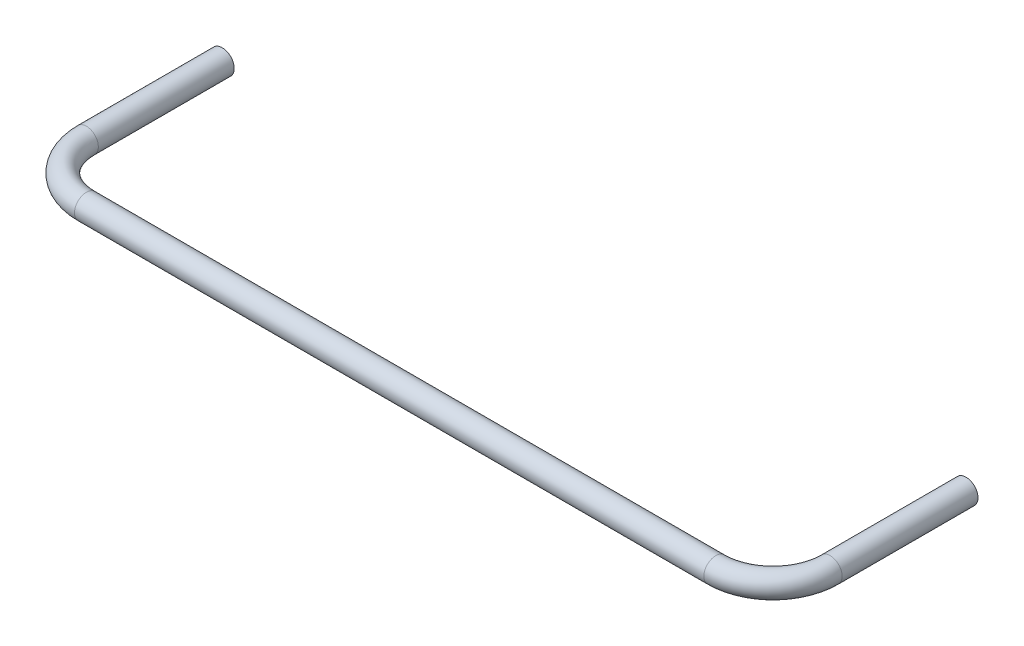
SolidWorks part; units mm, degrees
ref_plane "Front Plane" through (0, 0, 0) normal (0, 0, 1) x (1, 0, 0)
ref_plane "Top Plane" through (0, 0, 0) normal (0, 1, 0) x (1, 0, 0)
ref_plane "Right Plane" through (0, 0, 0) normal (1, 0, 0) x (0, 0, -1)
sketch "Sketch1" plane through (0, 0, 0) normal (0, 1, 0) x (1, 0, 0)
  line L0 (-220.025, -135) -> (220.025, -135)
  line L1 (-260.025, -95) -> (-260.025, 0)
  line L2 (260.025, -95) -> (260.025, 0)
  arc A0 (260.025, -95) -> (220.025, -135) centre (220.025, -95) cw
  arc A1 (-220.025, -135) -> (-260.025, -95) centre (-220.025, -95) cw
  point P10 (260.025, -135)
  point P13 (-260.025, -135)
  dimension "D4" = 40
  dimension "D1" = 520.05
  dimension "D2" = 135
  dimension "D3" = 260.025
sketch "Sketch2" plane through (0, 0, 0) normal (0, 0, 1) x (1, 0, 0)
  circle A0 centre (260.025, 0) radius 8.35
  dimension "D1" = 16.7
sweep "Sweep1" add profiles "Sketch2" path "Sketch1"
